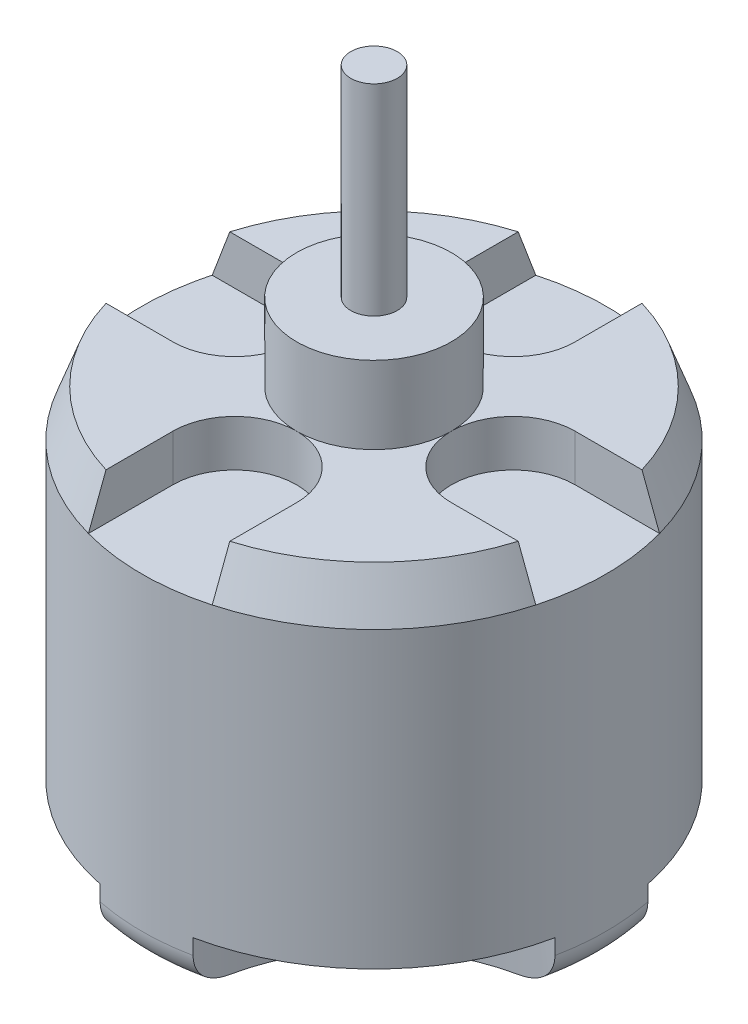
SolidWorks part; units mm, degrees
ref_plane "Plan de face" through (0, 0, 0) normal (0, 0, 1) x (1, 0, 0)
ref_plane "Plan de dessus" through (0, 0, 0) normal (0, 1, 0) x (1, 0, 0)
ref_plane "Plan de droite" through (0, 0, 0) normal (1, 0, 0) x (0, 0, -1)
sketch "Esquisse1" plane through (0, 0, 0) normal (0, 0, 1) x (1, 0, 0)
  line L0 (0, 23) -> (0, -20)
  line L1 (-1.5, -20) -> (-15, -20)
  line L2 (-15, -20) -> (-15, 5)
  line L3 (-15, 5) -> (-5, 5)
  line L4 (-5, 5) -> (-5, 10)
  line L5 (-5, 10) -> (-1.5, 10)
  line L6 (-1.5, 10) -> (-1.5, 23)
  line L7 (-1.5, 23) -> (0, 23)
  line L8 (0, -20) -> (0, -22)
  line L9 (0, -22) -> (-1.5, -22)
  line L10 (-1.5, -22) -> (-1.5, -20)
  dimension "D1" = 15
  dimension "D2" = 1.5
  dimension "D3" = 3.5
  dimension "D4" = 43
  dimension "D5" = 25
  dimension "D6" = 5
  dimension "D7" = 20
  dimension "D8" = 2
  dimension "D9" = 1.5
revolve "Révolution1" add sketch "Esquisse1" angle 360 about L0
chamfer "Chanfrein1" distance 3 angle 20 1 edges at (-15, 5, 0)
fillet "Congé1" radius 2 1 edges at (-15, -20, 0)
sketch "Esquisse2" plane through (0, 5, 0) normal (0, 1, 0) x (1, 0, 0)
  line L0 (-4, 9) -> (-4, 19)
  line L1 (-4, 19) -> (4, 19)
  line L2 (4, 19) -> (4, 9)
  line L3 (9, 4) -> (19, 4)
  line L4 (19, 4) -> (19, -4)
  line L5 (19, -4) -> (9, -4)
  line L6 (4, -9) -> (4, -19)
  line L7 (4, -19) -> (-4, -19)
  line L8 (-4, -19) -> (-4, -9)
  line L9 (-9, -4) -> (-19, -4)
  line L10 (-19, -4) -> (-19, 4)
  line L11 (-19, 4) -> (-9, 4)
  arc A0 (-4, 9) -> (4, 9) centre (0, 9) ccw
  circle A1 centre (0, 0) radius 5 construction
  arc A2 (9, 4) -> (9, -4) centre (9, 0) ccw
  arc A3 (4, -9) -> (-4, -9) centre (0, -9) ccw
  arc A4 (-9, -4) -> (-9, 4) centre (-9, 0) ccw
  dimension "D1" = 8
  dimension "D2" = 4
  dimension "D3" = 10
  dimension "D4" = 4
extrude "Enlèv. mat.-Extru.1" cut sketch "Esquisse2" against normal blind 3
sketch "Esquisse3" plane through (0, -20, 0) normal (0, -1, 0) x (1, 0, 0)
  line L0 (-3, 15) -> (-3, -15) construction
  line L1 (3, 15) -> (3, -15) construction
  line L2 (-15, 3) -> (15, 3) construction
  line L3 (-15, -3) -> (15, -3) construction
  arc A0 (-15, 3) -> (-3, 15) centre (-15, 15) ccw
  arc A1 (3, 15) -> (15, 3) centre (15, 15) ccw
  arc A2 (15, -3) -> (3, -15) centre (15, -15) ccw
  arc A3 (-15, -3) -> (-3, -15) centre (-15, -15) cw
  circle A4 centre (0, 9) radius 1.5
  circle A5 centre (0, -9) radius 1.5
  circle A6 centre (9, 0) radius 1.5
  circle A7 centre (-9, 0) radius 1.5
  arc A8 (-15, 3) -> (-3, 15) centre (-6.4869, 6.4869) cw
  arc A9 (-15, -3) -> (-3, -15) centre (-6.0335, -6.0335) ccw
  arc A10 (3, -15) -> (15, -3) centre (5.8989, -5.8989) ccw
  arc A11 (15, 3) -> (3, 15) centre (6.3169, 6.3169) ccw
  dimension "D3" = 3
  dimension "D4" = 3
  dimension "D6" = 3
  dimension "D13" = 3
  dimension "D2" = 3
  dimension "D5" = 30
  dimension "D7" = 30
  dimension "D8" = 15
  dimension "D9" = 30
  dimension "D10" = 30
  dimension "D11" = 15
  dimension "D12" = 15
  dimension "D14" = 9
  dimension "D15" = 9
  dimension "D16" = 9
  dimension "D17" = 9
extrude "Enlèv. mat.-Extru.2" cut sketch "Esquisse3" against normal blind 3
sketch "Esquisse4" plane through (0, -20, 0) normal (0, -1, 0) x (1, 0, 0)
  circle A0 centre (0, 0) radius 1.5
  circle A1 centre (0, 0) radius 5
  dimension "D1" = 10
extrude "Enlèv. mat.-Extru.3" cut sketch "Esquisse4" against normal blind 1
